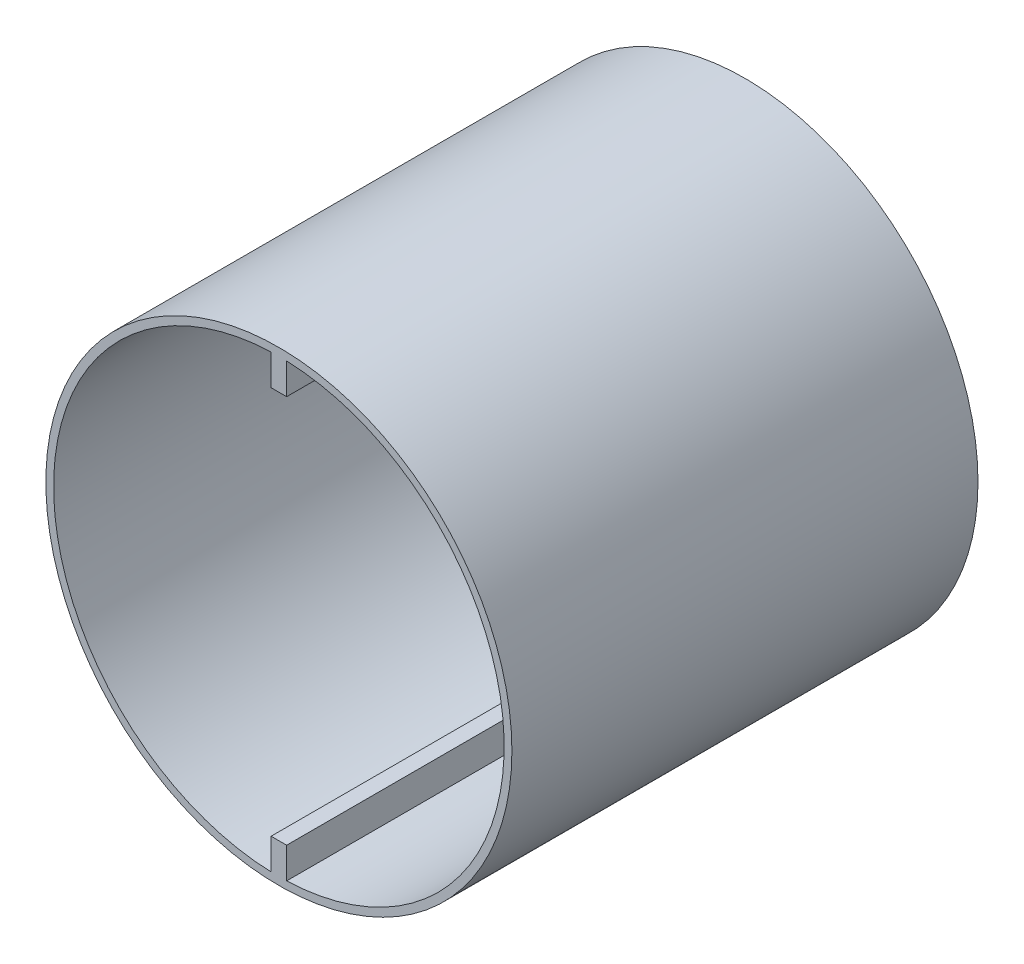
SolidWorks part; units mm, degrees
ref_plane "Plan de face" through (0, 0, 0) normal (0, 0, 1) x (1, 0, 0)
ref_plane "Plan de dessus" through (0, 0, 0) normal (0, 1, 0) x (1, 0, 0)
ref_plane "Plan de droite" through (0, 0, 0) normal (1, 0, 0) x (0, 0, -1)
sketch "Esquisse1" plane through (0, 0, 0) normal (0, 0, 1) x (1, 0, 0)
  line L0 (1, -15.0065) -> (1, -3.3541)
  line L1 (1, 29.5) -> (-1, 29.5)
  line L2 (-1, 29.5) -> (-1, 3.3541)
  line L3 (-1, -29.5) -> (1, -29.5)
  line L4 (1, -29.5) -> (1, -15.0065)
  line L5 (-1, -3.3541) -> (-1, -29.5)
  line L6 (1, 3.3541) -> (1, 29.5)
  arc A0 (-1, 3.3541) -> (-1, -3.3541) centre (0, 0) ccw
  arc A1 (1, -3.3541) -> (1, 3.3541) centre (0, 0) ccw
  dimension "D1" = 7
  dimension "D6" = 15.0065
  dimension "D2" = 59
  dimension "D3" = 29.5
  dimension "D4" = 2
  dimension "D5" = 1
extrude "Boss.-Extru.1" add sketch "Esquisse1" along normal blind 60
sketch "Esquisse2" plane through (0, 0, 60) normal (0, 0, 1) x (1, 0, 0)
  circle A0 centre (0, 0) radius 30
  circle A1 centre (0, 0) radius 29
  dimension "D1" = 60
  dimension "D2" = 58
extrude "Boss.-Extru.2" add sketch "Esquisse2" against normal blind 60
sketch "Esquisse3" plane through (0, 0, 60) normal (0, 0, 1) x (1, 0, 0)
  circle A0 centre (0, 0) radius 25
  dimension "D1" = 50
extrude "Enlèv. mat.-Extru.1" cut sketch "Esquisse3" against normal blind 27
sketch "Esquisse4" plane through (-1, 0, 0) normal (-1, 0, 0) x (0, 0, 1)
sketch "Esquisse6" plane through (0, 0, 33) normal (0, 0, 1) x (1, 0, 0)
  circle A0 centre (0, 0) radius 2.225
  dimension "D1" = 4.45
extrude "Enlèv. mat.-Extru.3" cut sketch "Esquisse6" against normal blind 2
sketch "Esquisse10" plane through (1, 0, 0) normal (1, 0, 0) x (0, 0, -1)
  line L0 (0, 0) -> (-46.88, 0) construction
  line L9 (-60, 30) -> (-60, -30) construction
  line L10 (-33, 25) -> (-60, 25) construction
  line L11 (-60, 25) -> (-18, 25) construction
  line L12 (-18, 25) -> (-18, -25) construction
  line L13 (-18, -25) -> (-60, -25) construction
  line L14 (-18, -3.3541) -> (-60, -3.3541)
  line L15 (-18, 25) -> (-60, 25)
  line L16 (-18, 25) -> (-18, 3.3541)
  line L17 (-18, 3.3541) -> (-60, 3.3541)
  line L18 (-60, 25) -> (-60, 3.3541)
  line L19 (-60, -25) -> (-60, -3.3541)
  line L20 (-18, -25) -> (-60, -25)
  line L21 (-18, -25) -> (-18, -3.3541)
  line L22 (-33, 3.3541) -> (-33, 24.98) construction
  dimension "D1" = 15
  dimension "D2" = 21.6459
extrude "Enlèv. mat.-Extru.7" cut sketch "Esquisse10" against normal blind 5
